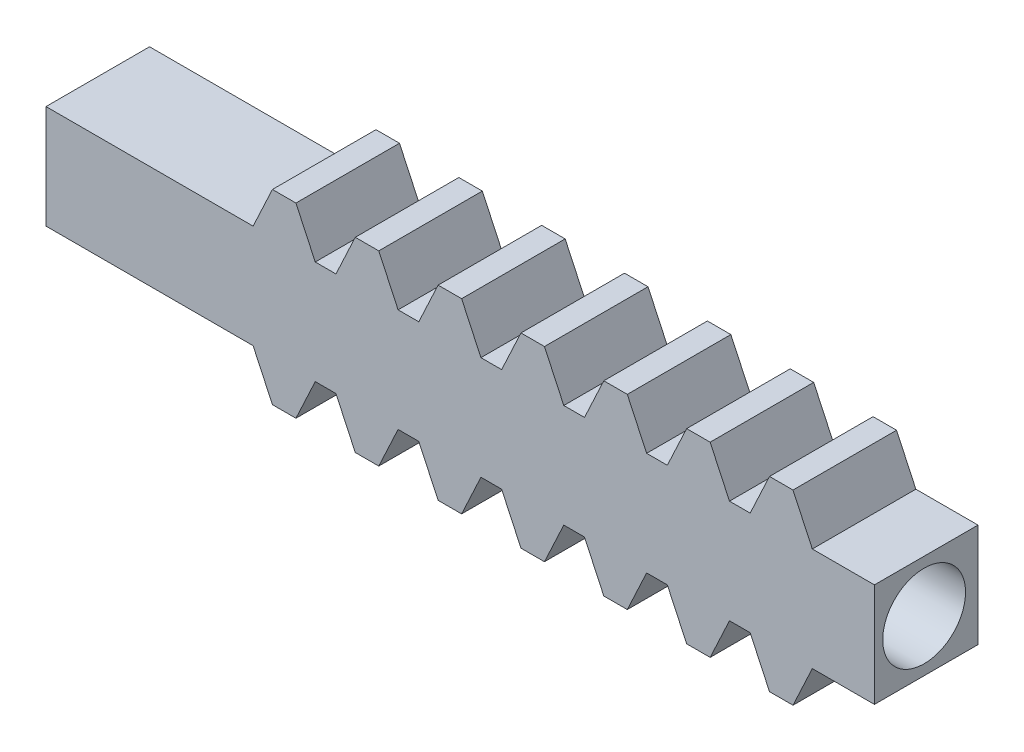
SolidWorks part; units mm, degrees
ref_plane "Front Plane" through (0, 0, 0) normal (0, 0, 1) x (1, 0, 0)
ref_plane "Top Plane" through (0, 0, 0) normal (0, 1, 0) x (1, 0, 0)
ref_plane "Right Plane" through (0, 0, 0) normal (1, 0, 0) x (0, 0, -1)
sketch "Sketch1" plane through (0, 0, 0) normal (0, 0, 1) x (1, 0, 0)
  line L0 (53, -5) -> (54, -5)
  line L1 (20, 0) -> (30, 0)
  line L3 (20, -5) -> (30, -5)
  line L4 (60, 0) -> (60, -5)
  line L5 (33, 0) -> (34, 0)
  line L6 (30, 0) -> (30.9326, 2)
  line L7 (33, 0) -> (32.0674, 2)
  line L8 (30.9326, 2) -> (32.0674, 2)
  line L9 (34, 0) -> (34.9326, 2)
  line L10 (34.9326, 2) -> (36.0674, 2)
  line L11 (37, 0) -> (36.0674, 2)
  line L12 (38, 0) -> (38.9326, 2)
  line L13 (38.9326, 2) -> (40.0674, 2)
  line L14 (41, 0) -> (40.0674, 2)
  line L15 (42, 0) -> (42.9326, 2)
  line L16 (42.9326, 2) -> (44.0674, 2)
  line L17 (45, 0) -> (44.0674, 2)
  line L18 (46, 0) -> (46.9326, 2)
  line L19 (46.9326, 2) -> (48.0674, 2)
  line L20 (49, 0) -> (48.0674, 2)
  line L21 (50, 0) -> (50.9326, 2)
  line L22 (50.9326, 2) -> (52.0674, 2)
  line L23 (53, 0) -> (52.0674, 2)
  line L24 (54, 0) -> (54.9326, 2)
  line L25 (54.9326, 2) -> (56.0674, 2)
  line L26 (57, 0) -> (56.0674, 2)
  line L27 (49, -5) -> (50, -5)
  line L28 (37, 0) -> (38, 0)
  line L29 (41, 0) -> (42, 0)
  line L30 (45, 0) -> (46, 0)
  line L31 (49, 0) -> (50, 0)
  line L32 (53, 0) -> (54, 0)
  line L33 (57, 0) -> (60, 0)
  line L34 (33, -5) -> (34, -5)
  line L35 (45, -5) -> (46, -5)
  line L36 (41, -5) -> (42, -5)
  line L37 (37, -5) -> (38, -5)
  line L38 (57, -5) -> (56.0674, -7)
  line L39 (54.9326, -7) -> (56.0674, -7)
  line L40 (54, -5) -> (54.9326, -7)
  line L41 (53, -5) -> (52.0674, -7)
  line L42 (50.9326, -7) -> (52.0674, -7)
  line L43 (50, -5) -> (50.9326, -7)
  line L44 (49, -5) -> (48.0674, -7)
  line L45 (46.9326, -7) -> (48.0674, -7)
  line L46 (46, -5) -> (46.9326, -7)
  line L47 (45, -5) -> (44.0674, -7)
  line L48 (42.9326, -7) -> (44.0674, -7)
  line L49 (42, -5) -> (42.9326, -7)
  line L50 (41, -5) -> (40.0674, -7)
  line L51 (38.9326, -7) -> (40.0674, -7)
  line L52 (38, -5) -> (38.9326, -7)
  line L53 (37, -5) -> (36.0674, -7)
  line L54 (34.9326, -7) -> (36.0674, -7)
  line L55 (34, -5) -> (34.9326, -7)
  line L56 (30.9326, -7) -> (32.0674, -7)
  line L57 (33, -5) -> (32.0674, -7)
  line L58 (30, -5) -> (30.9326, -7)
  line L59 (33, -5) -> (34, -5)
  line L60 (37, -5) -> (38, -5)
  line L61 (41, -5) -> (42, -5)
  line L62 (45, -5) -> (46, -5)
  line L63 (49, -5) -> (50, -5)
  line L64 (53, -5) -> (54, -5)
  line L65 (57, -5) -> (60, -5)
  line L66 (20, -5) -> (20, 0)
  point P63 (20, -2.5)
  dimension "D2" = 10
  dimension "D3" = 7
extrude "Boss-Extrude1" add sketch "Sketch1" along normal blind 5
sketch "Sketch3" plane through (60, 0, 0) normal (1, 0, 0) x (0, 0, -1)
  line L0 (-5, 0) -> (0, 0) construction
  circle A0 centre (-2.6017, -2.5) radius 2
  dimension "D1" = 4
  dimension "D2" = 2.5
extrude "Cut-Extrude1" cut sketch "Sketch3" against normal blind 5
sketch "Sketch4" plane through (0, 0, 0) normal (1, 0, 0) x (0, 0, -1)
  circle A0 centre (-2.6017, -2.5) radius 1
  circle A1 centre (-2.6017, -2.5) radius 2 construction
extrude "Cut-Extrude9" cut sketch "Sketch4" along normal through all
